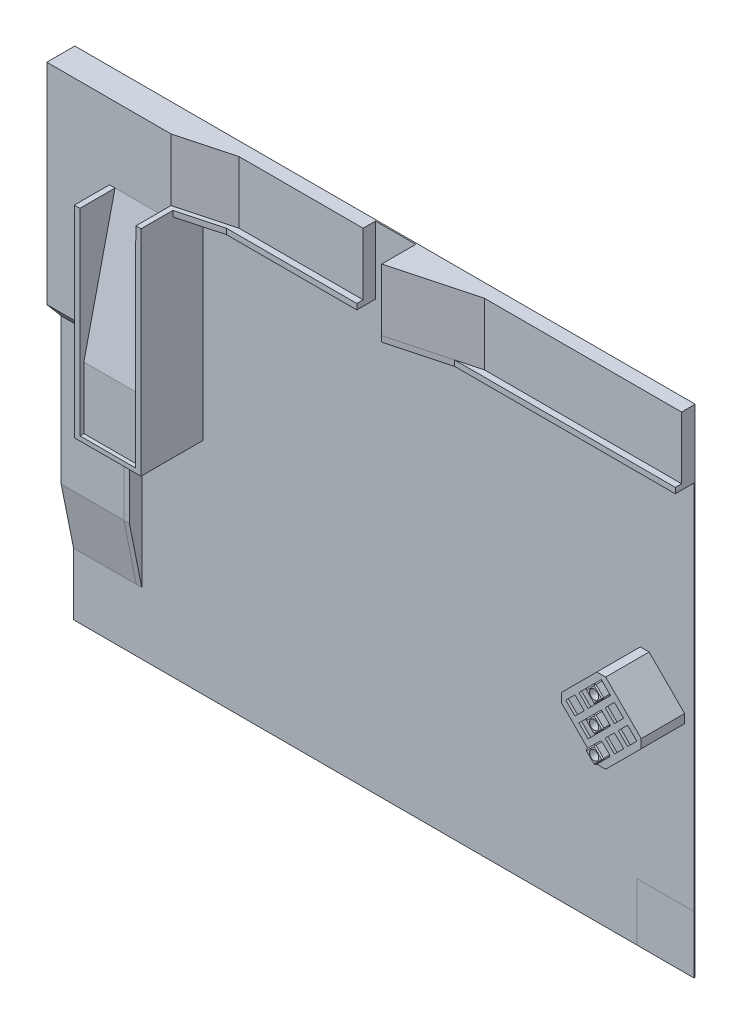
SolidWorks part; units mm, degrees
ref_plane "前视基准面" through (0, 0, 0) normal (0, 0, 1) x (1, 0, 0)
ref_plane "上视基准面" through (0, 0, 0) normal (0, 1, 0) x (1, 0, 0)
ref_plane "右视基准面" through (0, 0, 0) normal (1, 0, 0) x (0, 0, -1)
sketch "草图1" plane through (0, 0, 0) normal (0, 0, 1) x (1, 0, 0)
  line L1 (0, 0) -> (10000, 0)
  line L2 (0, 0) -> (0, 8000)
  line L3 (0, 8000) -> (10000, 8000)
  line L4 (10000, 0) -> (10000, 8000)
  line L5 (0, 0) -> (10000, 8000) construction
  line L6 (0, 8000) -> (10000, 0) construction
  point P4 (5000, 4000)
  dimension "D1" = 10000
  dimension "D2" = 8000
extrude "凸台-拉伸1" add sketch "草图1" along normal blind 20 contours L3 L4 L1 L2
sketch "草图2" plane through (0, 0, 20) normal (0, 0, 1) x (1, 0, 0)
  line L1 (10000, 8000) -> (5517, 8000)
  line L2 (10000, 8000) -> (10000, 7000)
  line L3 (10000, 7000) -> (5517, 7000)
  line L4 (5517, 8000) -> (5517, 7000)
  line L5 (10000, 8000) -> (5517, 7000) construction
  line L6 (10000, 7000) -> (5517, 8000) construction
  point P4 (7758.5, 7500)
  dimension "D1" = 4483
  dimension "D2" = 1000
extrude "凸台-拉伸2" add sketch "草图2" along normal blind 200 contours L3 L4 L1 L2
ref_plane "基准面2" through (0, 8000, 0) normal (0, 1, 0) x (1, 0, 0)
sketch "草图3" plane through (0, 8000, 0) normal (0, 1, 0) x (1, 0, 0)
  line L0 (5517, -220) -> (5517, -570)
  line L1 (5517, -220) -> (6823, -220)
  line L2 (10000, -220) -> (5517, -220) construction
  line L3 (6823, -220) -> (5517, -570)
extrude "凸台-拉伸3" add sketch "草图3" against normal blind 1000 contours L0 L3 L1
sketch "草图4" plane through (0, 0, 20) normal (0, 0, 1) x (1, 0, 0)
  line L0 (5517, 8000) -> (4867, 8000) construction
  line L1 (1265.4863, 8000) -> (-1265.4863, 8000) construction
sketch "草图5" plane through (0, 0, 20) normal (0, 0, 1) x (1, 0, 0)
  line L1 (4867, 8000) -> (2000, 8000)
  line L2 (4867, 8000) -> (4867, 7000)
  line L3 (4867, 7000) -> (2000, 7000)
  line L4 (2000, 8000) -> (2000, 7000)
  line L5 (4867, 8000) -> (2000, 7000) construction
  line L6 (4867, 7000) -> (2000, 8000) construction
  point P4 (3433.5, 7500)
  dimension "D1" = 2867
  dimension "D2" = 1000
extrude "凸台-拉伸4" add sketch "草图5" along normal blind 200 contours L3 L4 L1 L2
sketch "草图6" plane through (0, 8000, 0) normal (0, 1, 0) x (1, 0, 0)
  line L0 (2000, -220) -> (2865.4221, -220)
  line L1 (4867, -220) -> (2000, -220) construction
  line L2 (2865.4221, -220) -> (2000, -451.8891)
  line L3 (2000, -220) -> (2000, -451.8891)
  dimension "D1" = 15
extrude "凸台-拉伸5" add sketch "草图6" against normal blind 1000 contours L2 L3 L0
sketch "草图7" plane through (0, 0, 20) normal (0, 0, 1) x (1, 0, 0)
  line L0 (0, 0) -> (0, 8000) construction
  line L1 (2000, 8000) -> (0, 8000)
  line L2 (2000, 8000) -> (2000, 4617)
  line L3 (2000, 4617) -> (0, 4617)
  line L4 (0, 8000) -> (0, 4617)
  line L5 (2000, 8000) -> (0, 4617) construction
  line L6 (2000, 4617) -> (0, 8000) construction
  point P4 (1000, 6308.5)
  dimension "D1" = 3383
extrude "凸台-拉伸6" add sketch "草图7" along normal up to vertex (431.8891 mm away) up to point (2000, 8000, 451.8892)
sketch "草图8" plane through (0, 0, 20) normal (0, 0, 1) x (1, 0, 0)
  line L0 (0, 0) -> (0, 1000) construction
ref_plane "基准面3" through (2000, 0, 0) normal (1, 0, 0) x (0, 0, -1)
sketch "草图9" plane through (2000, 0, 0) normal (1, 0, 0) x (0, 0, -1)
  line L0 (-451.8891, 4617) -> (-451.8891, 6793.1479)
  line L1 (-451.8891, 4617) -> (-451.8891, 7000) construction
  line L2 (-451.8891, 6793.1479) -> (-954.2925, 4617)
  line L3 (-451.8891, 4617) -> (-954.2925, 4617)
  dimension "D1" = 13
extrude "凸台-拉伸7" add sketch "草图9" against normal up to vertex (2000 mm away) contours L2 L3 L0
sketch "草图10" plane through (0, 4617, 0) normal (0, -1, 0) x (1, 0, 0)
  line L0 (2000, 20) -> (1100, 20) construction
  line L1 (0, 20) -> (2000, 20) construction
  line L3 (1100, 20) -> (0, 20)
  line L4 (1100, 20) -> (1100, 954.2925)
  line L5 (1100, 954.2925) -> (0, 954.2925)
  line L6 (0, 20) -> (0, 954.2925)
  line L7 (1100, 20) -> (0, 954.2925) construction
  line L8 (1100, 954.2925) -> (0, 20) construction
  point P8 (550, 487.1462)
extrude "切除-拉伸1" cut sketch "草图10" against normal up to vertex (2176.1479 mm away) up to point (0, 6793.1479, 451.8892)
sketch "草图11" plane through (0, 6793.1479, 0) normal (0, -1, 0) x (1, 0, 0)
  line L1 (0, 451.8891) -> (1100, 451.8891)
  line L2 (0, 451.8891) -> (0, 20)
  line L3 (0, 20) -> (1100, 20)
  line L4 (1100, 451.8891) -> (1100, 20)
  line L5 (0, 451.8891) -> (1100, 20) construction
  line L6 (0, 20) -> (1100, 451.8891) construction
  point P4 (550, 235.9446)
extrude "凸台-拉伸8" add sketch "草图11" along normal up to vertex
sketch "草图12" plane through (0, 0, 20) normal (0, 0, 1) x (1, 0, 0)
  line L1 (1100, 4617) -> (2000, 4617)
  line L2 (1100, 4617) -> (1100, 3617)
  line L3 (1100, 3617) -> (2000, 3617)
  line L4 (2000, 4617) -> (2000, 3617)
  line L5 (1100, 4617) -> (2000, 3617) construction
  line L6 (1100, 3617) -> (2000, 4617) construction
  point P4 (1550, 4117)
  dimension "D1" = 900
  dimension "D2" = 1000
extrude "凸台-拉伸9" add sketch "草图12" along normal up to vertex (934.2925 mm away)
sketch "草图13" plane through (1100, 0, 0) normal (-1, 0, 0) x (0, 0, 1)
  line L0 (20, 4617) -> (20, 4342) construction
  line L1 (20, 4617) -> (20, 3617) construction
  line L2 (20, 4342) -> (220, 4342) construction
sketch "草图14" plane through (1100, 0, 0) normal (-1, 0, 0) x (0, 0, 1)
  line L0 (220, 4342) -> (220, 4617)
  line L1 (451.8891, 4617) -> (20, 4617) construction
  line L2 (220, 4617) -> (451.8891, 4617)
  line L3 (451.8891, 4617) -> (220, 4342)
extrude "凸台-拉伸10" add sketch "草图14" along normal up to vertex (1100 mm away)
sketch "草图15" plane through (0, 0, 20) normal (0, 0, 1) x (1, 0, 0)
  line L0 (0, 1000) -> (0, 2000) construction
  line L1 (0, 0) -> (0, 4617) construction
sketch "草图16" plane through (0, 4617, 0) normal (0, -1, 0) x (1, 0, 0)
  line L0 (1100, 20) -> (1100, 220) construction
  line L1 (0, 220) -> (1100, 220)
  line L2 (0, 220) -> (0, 20)
  line L3 (0, 20) -> (1100, 20)
  line L4 (1100, 220) -> (1100, 20)
  line L5 (0, 220) -> (1100, 20) construction
  line L6 (0, 20) -> (1100, 220) construction
  line L7 (0, 20) -> (10000, 20) construction
  point P4 (550, 120)
extrude "凸台-拉伸11" add sketch "草图16" along normal blind 2622
sketch "草图17" plane through (0, 0, 0) normal (-1, 0, 0) x (0, 0, 1)
  line L0 (20, 1995) -> (20, 1000)
  line L1 (20, 0) -> (20, 1000) construction
  line L2 (20, 1000) -> (20, 2000) construction
  line L3 (20, 1000) -> (220, 1995)
  line L4 (220, 1995) -> (20, 1995)
extrude "凸台-拉伸12" add sketch "草图17" against normal up to vertex (1100 mm away) up to point (1100, 1995, 220)
sketch "草图18" plane through (0, 0, 0) normal (0, 0, 1) x (1, 0, 0)
  line L0 (1100, 6793.1479) -> (1010, 6793.1479)
  line L1 (1010, 6793.1479) -> (1010, 3545.9064)
  line L2 (1010, 3545.9064) -> (2084.7482, 3545.9064)
  line L3 (2084.7482, 3545.9064) -> (2084.7482, 6793.1479)
  line L4 (2084.7482, 6793.1479) -> (2000, 6793.1479)
  line L5 (2000, 6793.1479) -> (2000, 7000) construction
  line L6 (2000, -533.0554) -> (2000, 533.0554) construction
  line L7 (2000, 6793.1479) -> (2000, 3617)
  line L8 (2000, 3617) -> (1100, 3617)
  line L9 (1100, 1995) -> (1100, 3617) construction
  line L10 (1100, 3617) -> (2000, 3617) construction
  line L11 (1100, 3617) -> (1100, 6793.1479)
extrude "凸台-拉伸13" add sketch "草图18" along normal blind 1018
sketch "草图19" plane through (0, 0, 220) normal (0, 0, 1) x (1, 0, 0)
  line L0 (1010, 3545.9064) -> (1010, 1995)
  line L1 (1100, 1995) -> (0, 1995) construction
  line L2 (1010, 1995) -> (1010, 1000)
  line L3 (1100, 1000) -> (0, 1000) construction
split line "分割线3"
sketch "草图20" plane through (0, 34.97, -173.9759) normal (0, -0.1971, 0.9804) x (1, 0, 0)
  line L0 (1010, 1999.2335) -> (1010, 984.332)
  line L1 (1100, 984.332) -> (0, 984.332) construction
split line "分割线4"
sketch "草图22" plane through (0, 6793.1479, 0) normal (0, 1, 0) x (1, 0, 0)
  line L1 (2084.7482, -1018) -> (2002.0722, -1018)
  line L2 (2084.7482, -1018) -> (2084.7482, -21.9109)
  line L3 (2084.7482, -21.9109) -> (2002.0722, -21.9109)
  line L4 (2002.0722, -1018) -> (2002.0722, -21.9109)
  line L5 (2084.7482, -1018) -> (2002.0722, -21.9109) construction
  line L6 (2084.7482, -21.9109) -> (2002.0722, -1018) construction
  point P4 (2043.4102, -519.9554)
extrude "凸台-拉伸14" add sketch "草图22" along normal up to vertex (206.8521 mm away)
sketch "草图23" plane through (2084.7482, 0, 0) normal (1, 0, 0) x (0, 0, -1)
  line L1 (-21.9109, 7000) -> (-1021.9109, 7000)
  line L2 (-21.9109, 7000) -> (-21.9109, 6910)
  line L3 (-21.9109, 6910) -> (-1021.9109, 6910)
  line L4 (-1021.9109, 7000) -> (-1021.9109, 6910)
  line L5 (-21.9109, 7000) -> (-1021.9109, 6910) construction
  line L6 (-21.9109, 6910) -> (-1021.9109, 7000) construction
  point P4 (-521.9109, 6955)
  dimension "D1" = 90
  dimension "D2" = 1000
extrude "凸台-拉伸15" add sketch "草图23" along normal up to vertex (2782.2518 mm away) contours L3 L4 L1 L2 up to point (4867, 7000, 220)
sketch "草图24" plane through (0, 7000, 0) normal (0, 1, 0) x (1, 0, 0)
  line L0 (2084.7482, -1018) -> (2084.7482, -504.3305)
  line L1 (2084.7482, -504.3305) -> (2764.3178, -321.5235)
  line L2 (2764.3178, -321.5235) -> (4867, -321.5235)
  line L3 (4867, -220) -> (4867, -1021.9109) construction
  line L4 (4867, -321.5235) -> (4867, -1021.9109)
  line L5 (4867, -1021.9109) -> (2084.7482, -1018)
extrude "切除-拉伸2" cut sketch "草图24" against normal blind 308
sketch "草图25" plane through (2084.7482, 0, 0) normal (1, 0, 0) x (0, 0, -1)
  line L1 (-1186.5825, 7045.2783) -> (-890.0245, 7045.2783)
  line L2 (-1186.5825, 7045.2783) -> (-1186.5825, 6808.5522)
  line L3 (-1186.5825, 6808.5522) -> (-890.0245, 6808.5522)
  line L4 (-890.0245, 7045.2783) -> (-890.0245, 6808.5522)
  line L5 (-1186.5825, 7045.2783) -> (-890.0245, 6808.5522) construction
  line L6 (-1186.5825, 6808.5522) -> (-890.0245, 7045.2783) construction
  point P4 (-1038.3035, 6926.9152)
extrude "切除-拉伸3" cut sketch "草图25" along normal blind 3067
sketch "草图26" plane through (10000, 0, 0) normal (1, 0, 0) x (0, 0, -1)
  line L1 (-321.5235, 7000) -> (-21.9109, 7000)
  line L2 (-321.5235, 7000) -> (-321.5235, 6910)
  line L3 (-321.5235, 6910) -> (-21.9109, 6910)
  line L4 (-21.9109, 7000) -> (-21.9109, 6910)
  line L5 (-321.5235, 7000) -> (-21.9109, 6910) construction
  line L6 (-321.5235, 6910) -> (-21.9109, 7000) construction
  point P4 (-171.7172, 6955)
extrude "凸台-拉伸16" add sketch "草图26" against normal up to vertex
sketch "草图27" plane through (0, 7000, 0) normal (0, -1, 0) x (1, 0, 0)
  line L0 (5517, 570) -> (5517, 321.5235)
  line L1 (5517, 570) -> (5517, 321.5235) construction
  line L2 (5517, 321.5235) -> (6444.1724, 321.5235)
  line L3 (5517, 321.5235) -> (10000, 321.5235) construction
  line L4 (6444.1724, 321.5235) -> (5517, 570) construction
  line L5 (6444.1724, 321.5235) -> (5517, 570)
extrude "凸台-拉伸17" add sketch "草图27" along normal up to vertex
sketch "草图28" plane through (512.2045, 0, 1911.2545) normal (0.2589, 0, 0.9659) x (0.9659, 0, -0.2589)
  line L0 (6141.2936, 7000) -> (5181.4034, 7000)
  line L1 (5181.4034, 6910) -> (5181.4034, 8000) construction
split line "分割线5"
sketch "草图29" plane through (0, 0, 20) normal (0, 0, 1) x (1, 0, 0)
  line L0 (2084.7482, 3545.9064) -> (2084.7482, 0) construction
  line L1 (0, 0) -> (10000, 0) construction
  line L2 (2084.7482, 0) -> (9084.7482, 0) construction
sketch "草图30" plane through (0, 0, 20) normal (0, 0, 1) x (1, 0, 0)
  line L0 (10000, 0) -> (10000, 7000) construction
  line L1 (9084.7482, 0) -> (10000, 0)
  line L2 (9084.7482, 0) -> (9084.7482, 928.3189)
  line L3 (9084.7482, 928.3189) -> (10000, 928.3189)
  line L4 (10000, 0) -> (10000, 928.3189)
  line L5 (9084.7482, 0) -> (10000, 928.3189) construction
  line L6 (9084.7482, 928.3189) -> (10000, 0) construction
  point P4 (9542.3741, 464.1594)
split line "分割线6"
sketch "草图31" plane through (0, 0, 20) normal (0, 0, 1) x (1, 0, 0)
  text T0 "A"
sketch "草图32" plane through (0, 0, 20) normal (0, 0, 1) x (1, 0, 0)
  line L0 (2084.7482, 3545.9064) -> (9920.2783, 3545.9064) construction
  line L1 (9206.1004, 4529.571) -> (9206.1004, 2562.2417) construction
  line L2 (9920.2783, 3545.9064) -> (9206.1004, 4260.0842)
  line L3 (9206.1004, 4260.0842) -> (8491.9226, 3545.9064)
  line L4 (8491.9226, 3545.9064) -> (9206.1004, 2831.7285)
  line L5 (9206.1004, 2831.7285) -> (9920.2783, 3545.9064)
  point P6 (9206.1004, 3545.9064)
  dimension "D1" = 45
  dimension "D2" = 1010
extrude "凸台-拉伸18" add sketch "草图32" along normal blind 700
chamfer "倒角1" distance 100 angle 45 4 edges at (9206.1004, 4260.0842, 370) (8491.9226, 3545.9064, 370) (9920.2783, 3545.9064, 370) (9206.1004, 2831.7285, 370)
sketch "草图34" plane through (0, 0, 720) normal (0, 0, 1) x (1, 0, 0)
  line L0 (9849.5676, 3616.617) -> (9135.3898, 2902.4392) construction
  line L1 (8562.6333, 3475.1957) -> (9276.8111, 4189.3735) construction
  line L2 (8562.6333, 3616.617) -> (9276.8111, 2902.4392) construction
  line L3 (9849.5676, 3475.1957) -> (9135.3898, 4189.3735) construction
sketch "草图35" plane through (0, 0, 720) normal (0, 0, 1) x (1, 0, 0)
  line L0 (8633.3439, 3545.9064) -> (8781.8364, 3694.3988)
  line L1 (8562.6333, 3475.1957) -> (9276.8111, 4189.3735) construction
  line L2 (8562.6333, 3616.617) -> (9276.8111, 2902.4392) construction
  line L3 (8781.8364, 3694.3988) -> (8930.3288, 3545.9064)
  line L4 (8930.3288, 3545.9064) -> (8781.8364, 3397.4139)
  line L5 (8781.8364, 3397.4139) -> (8633.3439, 3545.9064)
extrude "切除-拉伸5" cut sketch "草图35" against normal blind 42
pattern_linear "阵列(线性)2" count 3 spacing 300 along (0.7071, -0.7071, 0) count 3 spacing 300 along (0.7071, 0.7071, 0) of "切除-拉伸5"
sketch "草图36" plane through (0, 0, 678) normal (0, 0, 1) x (1, 0, 0)
  line L0 (9057.608, 3121.6423) -> (9206.1004, 3270.1347)
  line L1 (9206.1004, 3270.1347) -> (9354.5929, 3121.6423)
  line L2 (9354.5929, 3121.6423) -> (9206.1004, 2973.1499)
  line L3 (9057.608, 3121.6423) -> (9206.1004, 2973.1499) construction
  line L4 (9206.1004, 2973.1499) -> (9354.5929, 3121.6423) construction
  line L5 (9206.1004, 2973.1499) -> (9057.608, 3121.6423)
extrude "凸台-拉伸19" add sketch "草图36" along normal blind 158
chamfer "倒角4" distance 18 angle 45 4 edges at (9131.8542, 3195.8885, 836) (9280.3466, 3195.8885, 836) (9280.3466, 3047.3961, 836) (9131.8542, 3047.3961, 836)
chamfer "倒角5" distance 18 angle 45 4 edges at (9354.5929, 3121.6423, 769) (9206.1004, 3270.1347, 769) (9057.608, 3121.6423, 769) (9206.1004, 2973.1499, 769)
sketch "草图37" plane through (0, 0, 720) normal (0, 0, 1) x (1, 0, 0)
  line L0 (9057.608, 3545.9064) -> (9206.1004, 3397.4139)
  line L1 (9206.1004, 3397.4139) -> (9354.5929, 3545.9064)
  line L2 (9354.5929, 3545.9064) -> (9206.1004, 3694.3988)
  line L3 (9206.1004, 3694.3988) -> (9057.608, 3545.9064)
extrude "凸台-拉伸20" add sketch "草图37" along normal up to vertex (116 mm away) separate body
chamfer "倒角6" distance 18 angle 45 4 edges at (9280.3466, 3620.1526, 836) (9131.8542, 3620.1526, 836) (9131.8542, 3471.6601, 836) (9280.3466, 3471.6601, 836)
chamfer "倒角7" distance 18 angle 45 4 edges at (9206.1004, 3694.3988, 769) (9057.608, 3545.9064, 769) (9206.1004, 3397.4139, 769) (9354.5929, 3545.9064, 769)
sketch "草图38" plane through (0, 0, 720) normal (0, 0, 1) x (1, 0, 0)
  line L0 (9057.608, 3970.1704) -> (9206.1004, 4118.6629)
  line L1 (9206.1004, 4118.6629) -> (9354.5929, 3970.1704)
  line L2 (9354.5929, 3970.1704) -> (9206.1004, 3821.678)
  line L3 (9206.1004, 3821.678) -> (9057.608, 3970.1704)
extrude "凸台-拉伸21" add sketch "草图38" along normal up to vertex (116 mm away) separate body
chamfer "倒角8" distance 18 angle 45 8 edges at (9131.8542, 4044.4166, 836) (9206.1004, 4118.6629, 778) (9057.608, 3970.1704, 778) (9354.5929, 3970.1704, 778) (9280.3466, 4044.4166, 836) (9131.8542, 3895.9242, 836) (9206.1004, 3821.678, 778) (9280.3466, 3895.9242, 836)
sketch "草图41" plane through (0, 0, 836) normal (0, 0, 1) x (1, 0, 0)
  line L0 (9083.0639, 3970.1704) -> (9329.137, 3970.1704) construction
  circle A0 centre (9206.1004, 3970.1704) radius 75
  dimension "D1" = 150
extrude "切除-拉伸6" cut sketch "草图41" against normal blind 164
sketch "草图42" plane through (0, 0, 836) normal (0, 0, 1) x (1, 0, 0)
  line L0 (9083.0639, 3545.9064) -> (9329.137, 3545.9064) construction
  circle A0 centre (9206.1004, 3545.9064) radius 75
  dimension "D1" = 150
extrude "切除-拉伸7" cut sketch "草图42" against normal blind 164
sketch "草图43" plane through (0, 0, 836) normal (0, 0, 1) x (1, 0, 0)
  line L0 (9083.0639, 3121.6423) -> (9329.137, 3121.6423) construction
  circle A0 centre (9206.1004, 3121.6423) radius 75
  dimension "D1" = 150
extrude "切除-拉伸8" cut sketch "草图43" against normal blind 164
